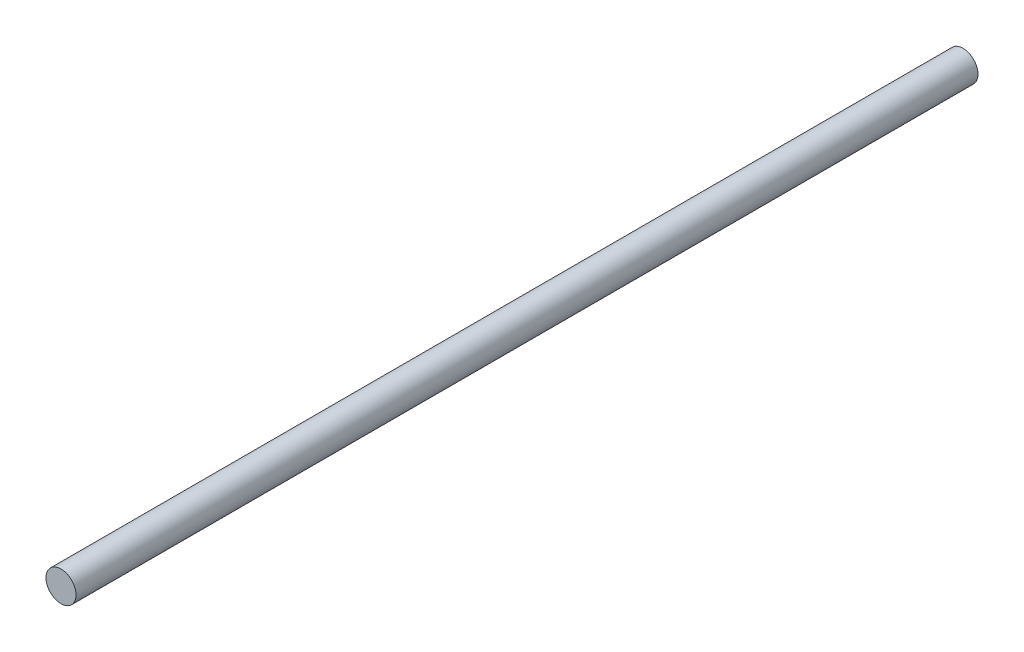
SolidWorks part; units mm, degrees
ref_plane "Front Plane" through (0, 0, 0) normal (0, 0, 1) x (1, 0, 0)
ref_plane "Top Plane" through (0, 0, 0) normal (0, 1, 0) x (1, 0, 0)
ref_plane "Right Plane" through (0, 0, 0) normal (1, 0, 0) x (0, 0, -1)
sketch "Sketch1" plane through (0, 0, 0) normal (0, 0, 1) x (1, 0, 0)
  circle A0 centre (0, 0) radius 6.35
  dimension "D1" = 12.7
extrude "Boss-Extrude1" add sketch "Sketch1" along normal mid plane 381
